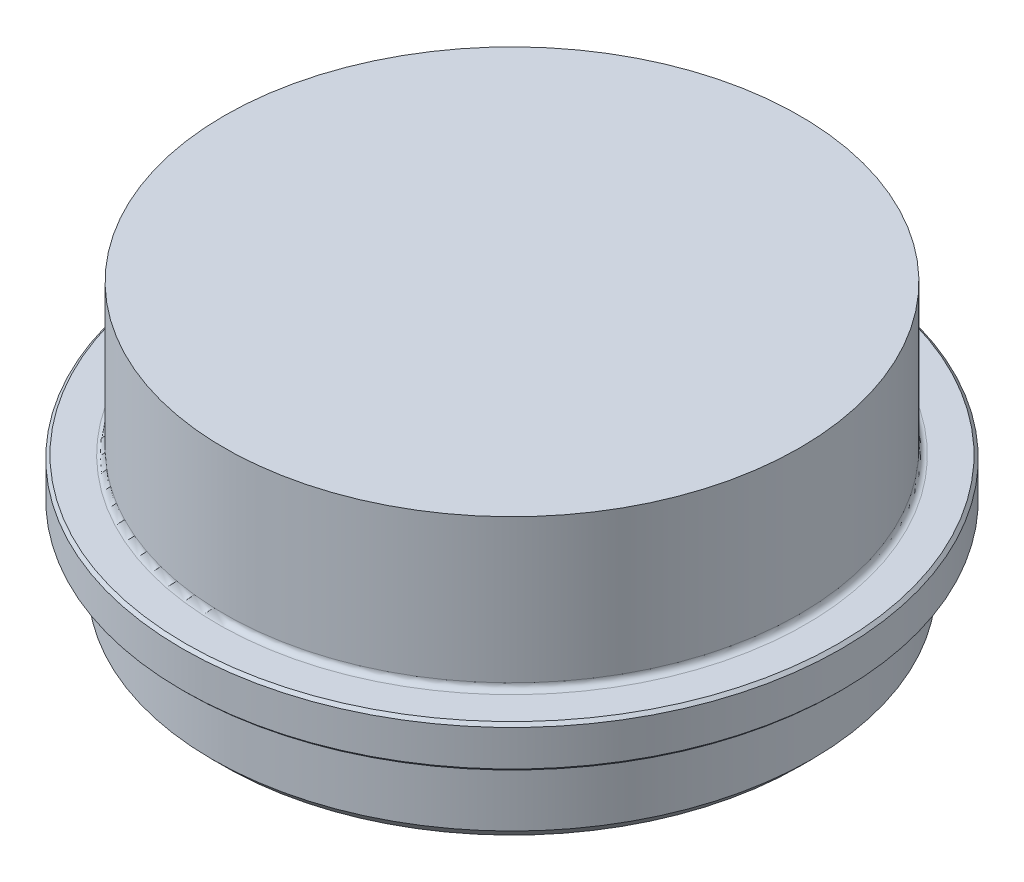
SolidWorks part; units mm, degrees
material "AISI 304"
ref_plane "Front Plane" through (0, 0, 0) normal (0, 0, 1) x (1, 0, 0)
ref_plane "Top Plane" through (0, 0, 0) normal (0, 1, 0) x (1, 0, 0)
ref_plane "Right Plane" through (0, 0, 0) normal (1, 0, 0) x (0, 0, -1)
sketch "Sketch1" plane through (0, 0, 0) normal (0, 0, 1) x (1, 0, 0)
  line L0 (0, -394.341) -> (0, 19322.7077) construction
  line L1 (-394.341, 0) -> (19322.7077, 0) construction
  line L2 (27.5, -12.5) -> (27.5, -16)
  line L3 (27.5, -16) -> (25, -16)
  line L4 (25, -16) -> (25, -23)
  line L5 (25, -23) -> (12.4, -23)
  line L6 (12.4, -23) -> (12.4, -16)
  line L7 (12.4, -16) -> (11.5, -16)
  line L8 (11.5, -16) -> (11.5, -5)
  line L9 (11.5, -5) -> (0, -5)
  line L10 (0, -5) -> (0, 0)
  line L11 (0, 0) -> (24, 0)
  line L12 (27.5, -12.5) -> (24, -12.5)
  line L13 (24, -12.5) -> (24, 0)
  point P7 (12.4, -19.5)
  dimension "D1" = 55
  dimension "D2" = 50
  dimension "D3" = 7
  dimension "D4" = 24.8
  dimension "D5" = 23
  dimension "D6" = 5
  dimension "D7" = 18
  dimension "D8" = 3.5
  dimension "D9" = 48
revolve "Revolve1" add sketch "Sketch1" angle 360 about L0
chamfer "Chamfer1" distance 1 angle 45 2 edges at (12.4, -23, 0) (25, -23, 0)
chamfer "Chamfer2" distance 0.25 angle 45 3 edges at (11.5, -16, 0) (27.5, -16, 0) (27.5, -12.5, 0)
fillet "Fillet1" radius 0.5 2 edges at (24, -12.5, 0) (11.5, -5, 0)
sketch "Sketch2" plane through (0, -23, 0) normal (0, -1, 0) x (1, 0, 0)
  line L0 (0, -1000) -> (0, 49000) construction
  line L1 (-1000, 0) -> (49000, 0) construction
  line L3 (-14.1421, -14.1421) -> (14.1421, -14.1421) construction
  line L4 (-14.1421, -14.1421) -> (-14.1421, 14.1421) construction
  line L5 (-14.1421, 14.1421) -> (14.1421, 14.1421) construction
  line L6 (14.1421, -14.1421) -> (14.1421, 14.1421) construction
  line L7 (-14.1421, -14.1421) -> (14.1421, 14.1421) construction
  line L8 (-14.1421, 14.1421) -> (14.1421, -14.1421) construction
  circle A0 centre (14.1421, 14.1421) radius 2.5
  circle A1 centre (-14.1421, 14.1421) radius 2.5
  circle A2 centre (14.1421, -14.1421) radius 2.5
  circle A3 centre (-14.1421, -14.1421) radius 2.5
  circle A4 centre (0, 20) radius 3
  circle A5 centre (0, 0) radius 12.4 construction
  circle A6 centre (0, 0) radius 12.4 construction
  point P4 (0, 0)
  point P21 (0, 12.4)
  dimension "D2" = 5
  dimension "D4" = 6
  dimension "D1" = 40
  dimension "D3" = 7.6
extrude "Cut-Extrude1" cut sketch "Sketch2" against normal blind 14
cosmetic thread "Cosmetic Thread1" parameters "D1"=10, "D2"=6
cosmetic thread "Cosmetic Thread2" parameters "D1"=5, "D2"=6
cosmetic thread "Cosmetic Thread3" parameters "D1"=5, "D2"=6
cosmetic thread "Cosmetic Thread4" parameters "D1"=5, "D2"=6
